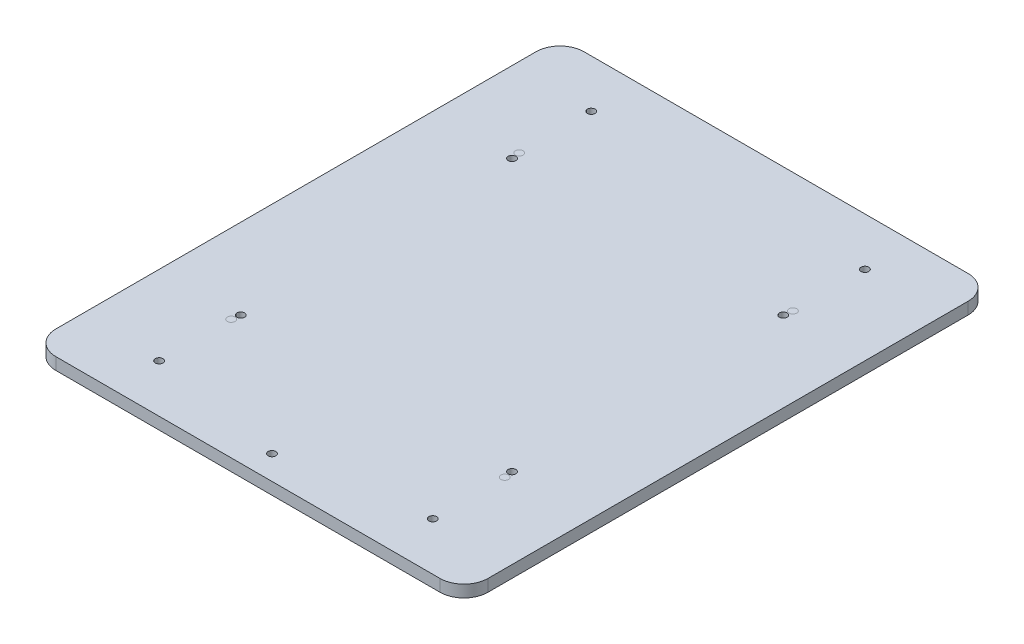
SolidWorks part; units mm, degrees
ref_plane "前视基准面" through (0, 0, 0) normal (0, 0, 1) x (1, 0, 0)
ref_plane "上视基准面" through (0, 0, 0) normal (0, 1, 0) x (1, 0, 0)
ref_plane "右视基准面" through (0, 0, 0) normal (1, 0, 0) x (0, 0, -1)
sketch "草图1" plane through (0, 0, 0) normal (0, 1, 0) x (1, 0, 0)
  line L0 (-114.0741, 75.3411) -> (-81.0741, 75.3411) construction
  line L1 (-104.0741, 85.3411) -> (55.9259, 85.3411)
  line L2 (-114.0741, 75.3411) -> (-114.0741, -124.6589)
  line L3 (-104.0741, -134.6589) -> (55.9259, -134.6589)
  line L4 (65.9259, 75.3411) -> (65.9259, -124.6589)
  line L5 (65.9259, 75.3411) -> (32.9259, 75.3411) construction
  line L6 (-114.0741, -124.6589) -> (-81.0741, -124.6589) construction
  line L7 (65.9259, -124.6589) -> (32.9259, -124.6589) construction
  line L8 (-81.0741, 85.3411) -> (-81.0741, 35.3411) construction
  line L9 (-81.0741, -134.6589) -> (-81.0741, -84.6589) construction
  line L10 (-81.0741, 35.3411) -> (32.9259, 35.3411) construction
  line L11 (32.9259, 35.3411) -> (32.9259, -84.6589) construction
  arc A0 (-104.0741, 85.3411) -> (-114.0741, 75.3411) centre (-104.0741, 75.3411) ccw
  arc A1 (55.9259, 85.3411) -> (65.9259, 75.3411) centre (55.9259, 75.3411) cw
  arc A2 (55.9259, -134.6589) -> (65.9259, -124.6589) centre (55.9259, -124.6589) ccw
  arc A3 (-114.0741, -124.6589) -> (-104.0741, -134.6589) centre (-104.0741, -124.6589) ccw
  circle A4 centre (-81.0741, 35.3411) radius 1.6
  circle A5 centre (32.9259, 35.3411) radius 1.6
  circle A6 centre (32.9259, -84.6589) radius 1.6
  circle A7 centre (-81.0741, -84.6589) radius 1.6
  point P6 (-114.0741, 85.3411)
  point P9 (65.9259, 85.3411)
  point P14 (-114.0741, -134.6589)
  dimension "D3" = 10
  dimension "D4" = 10
  dimension "D5" = 10
  dimension "D6" = 10
  dimension "D1" = 220
  dimension "D2" = 180
  dimension "D7" = 33
extrude "凸台-拉伸1" add sketch "草图1" along normal blind 5
sketch "草图4" plane through (0, 5, 0) normal (0, 1, 0) x (1, 0, 0)
  line L0 (-24.0741, 85.3411) -> (-24.0741, 75.3411) construction
  line L1 (55.9259, 85.3411) -> (-104.0741, 85.3411) construction
  line L2 (-24.0741, 85.3411) -> (-24.0741, -134.6589) construction
  line L3 (-104.0741, -134.6589) -> (55.9259, -134.6589) construction
  line L4 (65.9259, -24.6589) -> (-114.0741, -24.6589) construction
  line L5 (65.9259, -124.6589) -> (65.9259, 75.3411) construction
  line L6 (-114.0741, 75.3411) -> (-114.0741, -124.6589) construction
  line L7 (-24.0741, -24.6589) -> (32.6259, -24.6589) construction
  line L8 (-24.0741, -24.6589) -> (-80.7741, -24.6589) construction
  line L9 (-24.0741, -24.6589) -> (-24.0741, 31.8411) construction
  line L10 (-24.0741, 31.8411) -> (32.6259, 31.8411) construction
  line L11 (32.6259, 31.8411) -> (32.6259, -24.6589) construction
  line L12 (-24.0741, -24.6589) -> (-24.0741, -81.1589) construction
  line L13 (-24.0741, -81.1589) -> (32.6259, -81.1589) construction
  line L14 (32.6259, -81.1589) -> (32.6259, -24.6589) construction
  line L15 (32.6259, -24.6589) -> (-80.7741, -24.6589) construction
  line L16 (-80.7741, -24.6589) -> (-80.7741, -81.1589) construction
  line L17 (-80.7741, -81.1589) -> (-24.0741, -81.1589) construction
  line L18 (-80.7741, -24.6589) -> (-80.7741, 31.8411) construction
  line L19 (-80.7741, 31.8411) -> (-24.0741, 31.8411) construction
  line L20 (-81.0741, 35.3411) -> (-81.0741, 65.3411) construction
  line L21 (32.9259, 35.3411) -> (32.9259, 65.3411)
  line L22 (-81.0741, -84.6589) -> (-81.0741, -114.6589) construction
  line L23 (32.9259, -84.6589) -> (32.9259, -114.6589) construction
  circle A0 centre (-24.0741, 75.3411) radius 1.6
  circle A1 centre (-81.0741, 65.3411) radius 1.6
  circle A2 centre (32.9259, 65.3411) radius 1.6
  circle A3 centre (-81.0741, -114.6589) radius 1.6
  circle A4 centre (32.9259, -114.6589) radius 1.6
  circle A5 centre (-81.0741, 35.3411) radius 1.6
  circle A6 centre (32.9259, 35.3411) radius 1.6
  circle A7 centre (32.9259, -84.6589) radius 1.6
  circle A8 centre (-81.0741, -84.6589) radius 1.6
  circle A9 centre (-80.7741, 31.8411) radius 1.6
  circle A10 centre (32.6259, 31.8411) radius 1.6
  circle A11 centre (32.6259, -81.1589) radius 1.6
  circle A12 centre (-80.7741, -81.1589) radius 1.6
  dimension "D1" = 3.2
  dimension "D2" = 56.7
extrude "切除-拉伸2" cut sketch "草图4" against normal blind 10 contours A3 | A4 | A2 | A1
sketch "草图5" plane through (0, 5, 0) normal (0, 1, 0) x (1, 0, 0)
  circle A0 centre (-81.0741, 35.3411) radius 1.6
  circle A1 centre (32.9259, 35.3411) radius 1.6
  circle A2 centre (32.9259, -84.6589) radius 1.6
  circle A3 centre (-81.0741, -84.6589) radius 1.6
extrude "凸台-拉伸3" add sketch "草图5" against normal blind 5 separate body
sketch "草图6" plane through (0, 5, 0) normal (0, 1, 0) x (1, 0, 0)
  line L0 (-24.0741, 85.3411) -> (-24.0741, -134.6589) construction
  line L1 (55.9259, 85.3411) -> (-104.0741, 85.3411) construction
  line L2 (-104.0741, -134.6589) -> (55.9259, -134.6589) construction
  line L3 (-24.0741, -134.6589) -> (-114.0741, -24.6589) construction
  line L4 (-114.0741, 75.3411) -> (-114.0741, -124.6589) construction
  line L5 (-114.0741, -24.6589) -> (65.9259, -24.6589) construction
  line L6 (65.9259, -124.6589) -> (65.9259, 75.3411) construction
  line L7 (-24.0741, -24.6589) -> (32.4259, -24.6589) construction
  line L8 (-24.0741, -24.6589) -> (-80.5741, -24.6589) construction
  line L9 (-24.0741, -24.6589) -> (-24.0741, 31.8411) construction
  line L10 (-24.0741, -24.6589) -> (-24.0741, -81.1589) construction
  line L11 (-24.0741, 31.8411) -> (32.4259, 31.8411) construction
  line L12 (32.4259, 31.8411) -> (32.4259, -24.6589) construction
  line L13 (-24.0741, -81.1589) -> (-80.5741, -81.1589) construction
  line L14 (-80.5741, -81.1589) -> (-80.5741, -24.6589) construction
  line L15 (-24.0741, -81.1589) -> (32.4259, -81.1589) construction
  line L16 (32.4259, -81.1589) -> (32.4259, -24.6589) construction
  line L17 (-24.0741, 31.8411) -> (-80.5741, 31.8411) construction
  line L18 (-80.5741, 31.8411) -> (-80.5741, -24.6589) construction
  circle A0 centre (-80.5741, -81.1589) radius 1.6
  circle A1 centre (-80.5741, 31.8411) radius 1.6
  circle A2 centre (32.4259, 31.8411) radius 1.6
  circle A3 centre (32.4259, -81.1589) radius 1.6
extrude "切除-拉伸3" cut sketch "草图6" against normal blind 5
sketch "草图8" plane through (0, 0, 0) normal (0, -1, 0) x (1, 0, 0)
  line L0 (-24.0741, 134.6589) -> (-24.0741, 124.6589) construction
  line L1 (-104.0741, 134.6589) -> (55.9259, 134.6589) construction
  circle A0 centre (-24.0741, 124.6589) radius 1.6
extrude "切除-拉伸4" cut sketch "草图8" against normal blind 5
